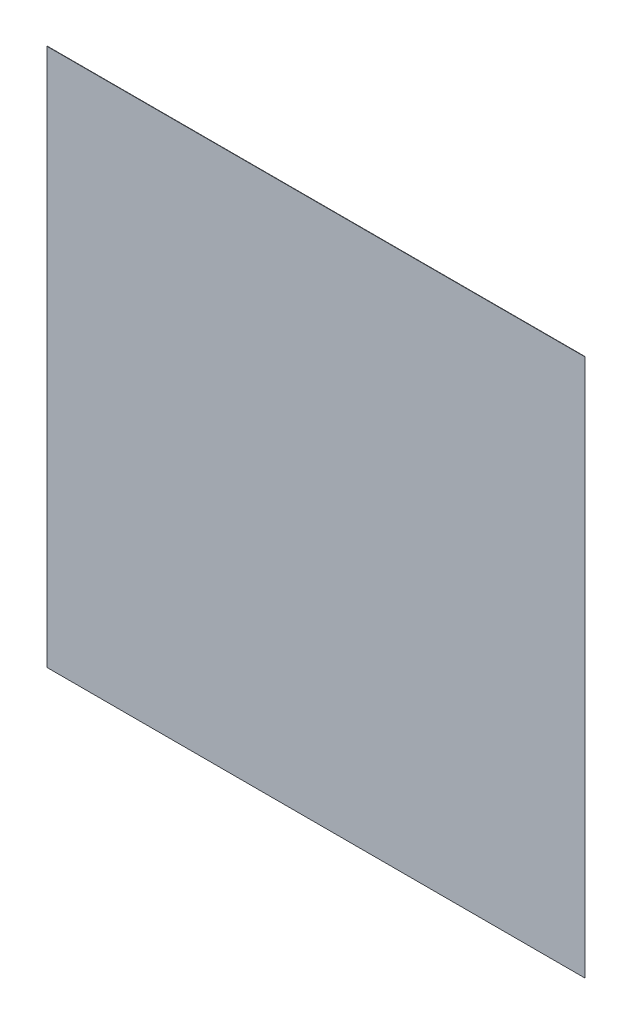
SolidWorks part; units mm, degrees
ref_plane "Front Plane" through (0, 0, 0) normal (0, 0, 1) x (1, 0, 0)
ref_plane "Top Plane" through (0, 0, 0) normal (0, 1, 0) x (1, 0, 0)
ref_plane "Right Plane" through (0, 0, 0) normal (1, 0, 0) x (0, 0, -1)
sketch "Sketch2" plane through (0, 0, 0) normal (0, 0, 1) x (1, 0, 0)
  line L1 (265, 265) -> (-265, 265)
  line L2 (265, 265) -> (265, -265)
  line L3 (265, -265) -> (-265, -265)
  line L4 (-265, 265) -> (-265, -265)
  line L5 (265, 265) -> (-265, -265) construction
  line L6 (265, -265) -> (-265, 265) construction
  point P0 (0, 0)
  dimension "D1" = 530
  dimension "D2" = 530
extrude "Boss-Extrude1" add sketch "Sketch2" along normal blind 0.35
